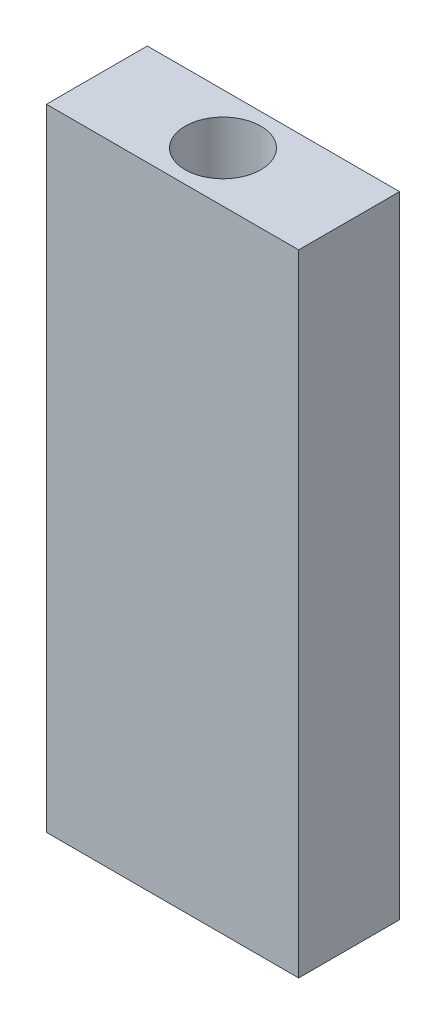
SolidWorks part; units mm, degrees
ref_plane "Front Plane" through (0, 0, 0) normal (0, 0, 1) x (1, 0, 0)
ref_plane "Top Plane" through (0, 0, 0) normal (0, 1, 0) x (1, 0, 0)
ref_plane "Right Plane" through (0, 0, 0) normal (1, 0, 0) x (0, 0, -1)
sketch "Sketch1" plane through (0, 0, 0) normal (0, 1, 0) x (1, 0, 0)
  line L1 (-5, 2) -> (5, 2)
  line L2 (-5, 2) -> (-5, -2)
  line L3 (-5, -2) -> (5, -2)
  line L4 (5, 2) -> (5, -2)
  circle A0 centre (0, 0) radius 1.5
  point P8 (0, 2)
  point P9 (-5, 0)
  dimension "D3" = 3
  dimension "D1" = 4
  dimension "D2" = 10
extrude "Boss-Extrude1" add sketch "Sketch1" along normal blind 25
